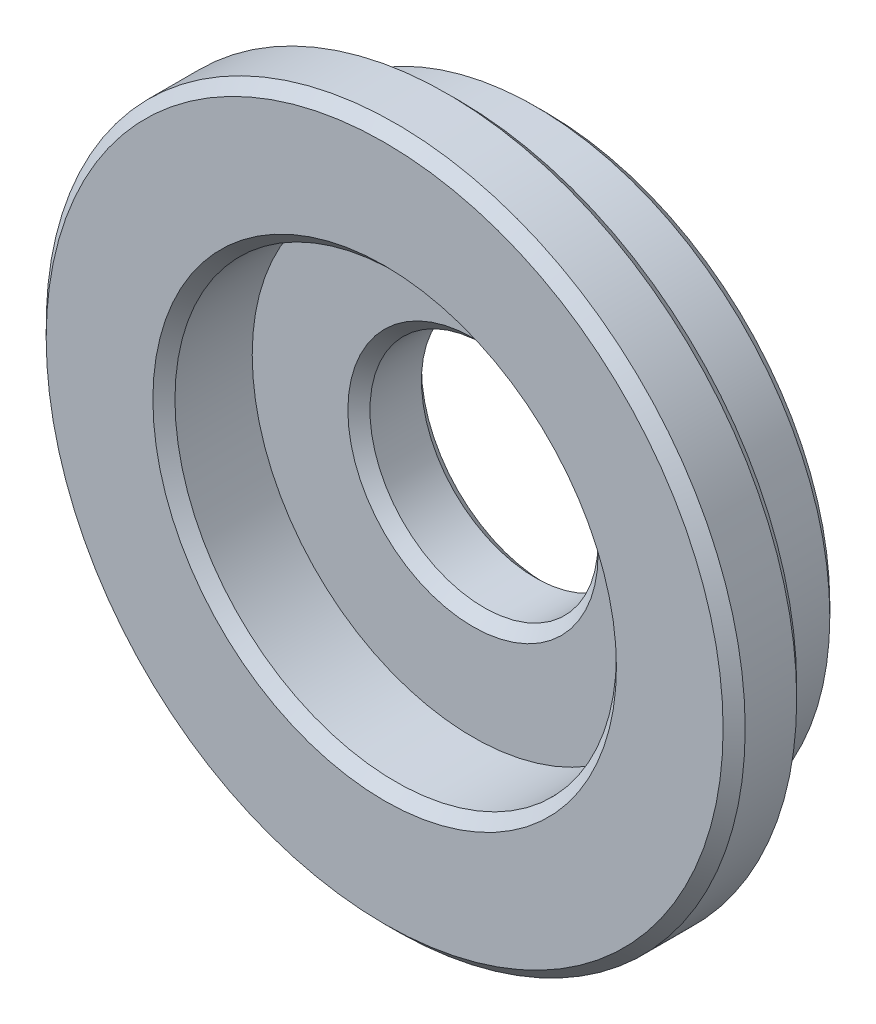
SolidWorks part; units mm, degrees
material "Aluminium"
ref_plane "Front Plane" through (0, 0, 0) normal (0, 0, 1) x (1, 0, 0)
ref_plane "Top Plane" through (0, 0, 0) normal (0, 1, 0) x (1, 0, 0)
ref_plane "Right Plane" through (0, 0, 0) normal (1, 0, 0) x (0, 0, -1)
sketch "Sketch1" plane through (0, 0, 0) normal (0, 1, 0) x (1, 0, 0)
  line L0 (3.15, -1) -> (4.6, -1)
  line L1 (4.6, -1) -> (4.75, -0.85)
  line L2 (4.75, -0.85) -> (4.75, -0.15)
  line L3 (4.75, -0.15) -> (4.6, 0)
  line L4 (4.6, 0) -> (4, 0)
  line L5 (4, 0) -> (4, 1.05)
  line L6 (4, 1.05) -> (3.85, 1.2)
  line L7 (3.85, 1.2) -> (1.7, 1.2)
  line L8 (1.7, 1.2) -> (1.55, 1.05)
  line L9 (1.55, 1.05) -> (1.55, 0.35)
  line L10 (1.55, 0.35) -> (1.7, 0.2)
  line L11 (1.7, 0.2) -> (3, 0.2)
  line L12 (3, 0.2) -> (3, -0.85)
  line L13 (3, -0.85) -> (3.15, -1)
  line L14 (0, 1.2) -> (0, -1) construction
revolve "Revolve1" add sketch "Sketch1" angle 360 about L14
